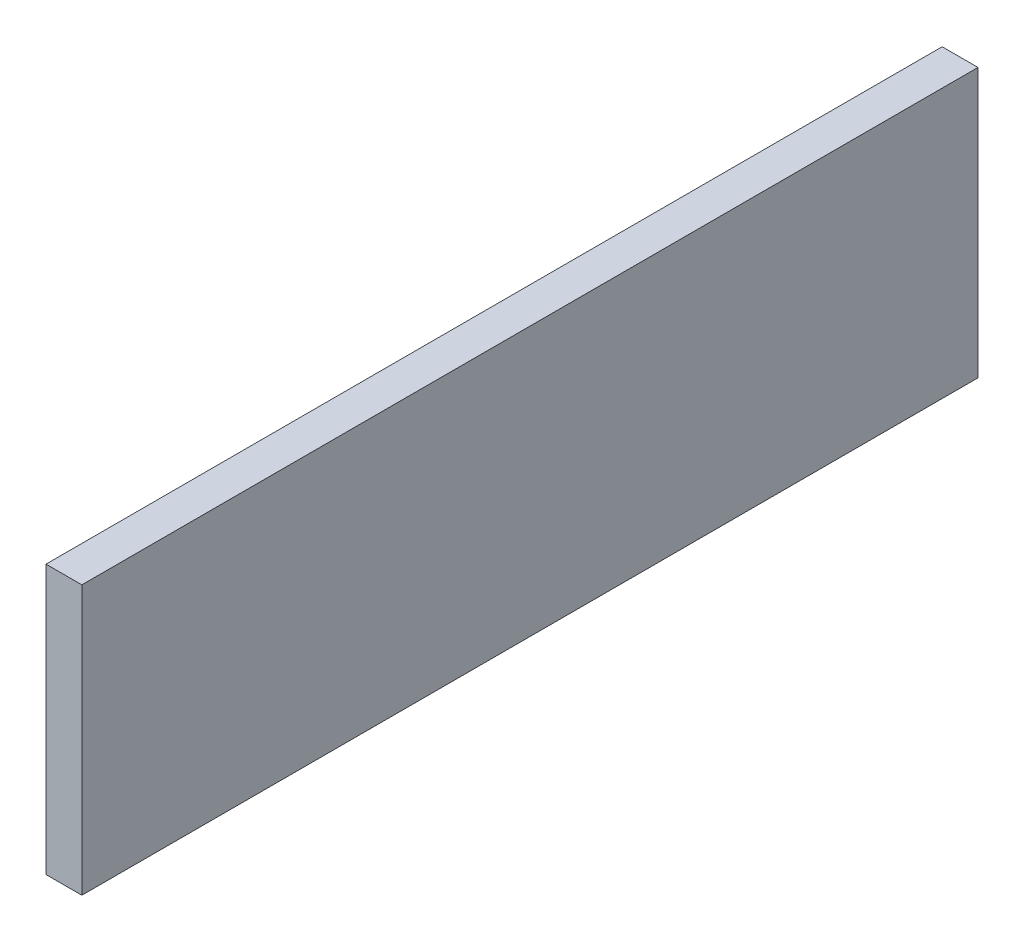
SolidWorks part; units mm, degrees
ref_plane "Front Plane" through (0, 0, 0) normal (0, 0, 1) x (1, 0, 0)
ref_plane "Top Plane" through (0, 0, 0) normal (0, 1, 0) x (1, 0, 0)
ref_plane "Right Plane" through (0, 0, 0) normal (1, 0, 0) x (0, 0, -1)
sketch "Sketch1" plane through (0, 0, 0) normal (1, 0, 0) x (0, 0, -1)
  line L1 (0, 0) -> (63.5, 0)
  line L2 (0, 0) -> (0, -19.05)
  line L3 (0, -19.05) -> (63.5, -19.05)
  line L4 (63.5, 0) -> (63.5, -19.05)
  dimension "D1" = 19.05
  dimension "D2" = 63.5
extrude "Boss-Extrude1" add sketch "Sketch1" along normal blind 2.54
